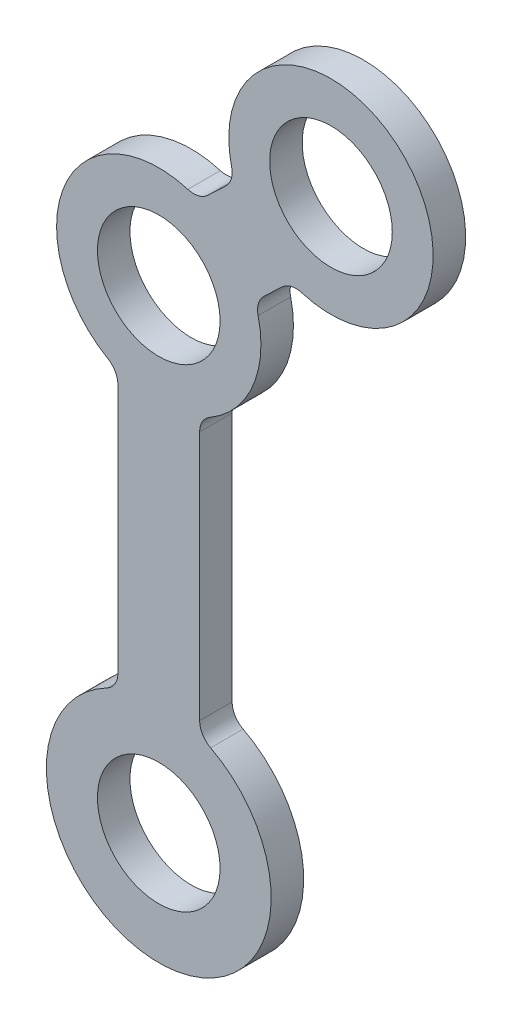
SolidWorks part; units mm, degrees
ref_plane "Front Plane" through (0, 0, 0) normal (0, 0, 1) x (1, 0, 0)
ref_plane "Top Plane" through (0, 0, 0) normal (0, 1, 0) x (1, 0, 0)
ref_plane "Right Plane" through (0, 0, 0) normal (1, 0, 0) x (0, 0, -1)
sketch "Sketch1" plane through (0, 0, 0) normal (0, 0, 1) x (1, 0, 0)
  line L0 (0, 0) -> (0, 23.1951) construction
  line L1 (0, 23.1951) -> (8.4255, 31.1817) construction
  line L3 (5.147, 25.3183) -> (6.0303, 26.1555)
  line L4 (-2, 5.7663) -> (-2, 17.9989)
  line L5 (2.3952, 28.2213) -> (3.2785, 29.0585)
  line L6 (-2, 24.055) -> (7.0496, 32.6332) construction
  line L7 (-2, 0) -> (-2, 24.055) construction
  line L8 (2, 5.7663) -> (2, 17.9989)
  line L9 (2, 0) -> (2, 22.3352) construction
  line L10 (2, 22.3352) -> (9.8014, 29.7302) construction
  circle A0 centre (0, 0) radius 3
  arc A1 (4.1174, 26.8416) -> (4.1166, 26.8425) centre (0, 23.1951) ccw
  circle A2 centre (0, 23.1951) radius 3
  arc A3 (2.5, 18.865) -> (4.8625, 24.3596) centre (0, 23.1951) ccw
  arc A4 (7.0028, 26.3884) -> (3.563, 30.0172) centre (8.4255, 31.1817) ccw
  arc A5 (1.4227, 27.9884) -> (-2.5, 18.865) centre (0, 23.1951) ccw
  arc A6 (-2.5385, 4.8792) -> (2.5385, 4.8792) centre (0, 0) ccw
  arc A7 (2, 17.9989) -> (2.5, 18.865) centre (3, 17.9989) cw
  circle A8 centre (8.4255, 31.1817) radius 3
  arc A9 (5.147, 25.3183) -> (4.8625, 24.3596) centre (5.835, 24.5925) ccw
  arc A10 (2.3952, 28.2213) -> (1.4227, 27.9884) centre (1.7073, 28.9471) cw
  arc A11 (3.563, 30.0172) -> (3.2785, 29.0585) centre (2.5905, 29.7843) cw
  arc A12 (7.0028, 26.3884) -> (6.0303, 26.1555) centre (6.7182, 25.4298) ccw
  arc A13 (-2.5385, 4.8792) -> (-2, 5.7663) centre (-3, 5.7663) ccw
  arc A14 (2.5385, 4.8792) -> (2, 5.7663) centre (3, 5.7663) cw
  arc A15 (-2, 17.9989) -> (-2.5, 18.865) centre (-3, 17.9989) ccw
  point P22 (0.3476, 28.6841)
  point P28 (2, 18.0716)
  point P31 (1.9499, 27.7992)
  point P32 (-2, 18.0716)
  dimension "D1" = 23.1951
  dimension "D4" = 2
  dimension "D6" = 1
  dimension "D7" = 1
  dimension "D8" = 1
  dimension "D9" = 1
  dimension "D10" = 32.3
  dimension "D11" = 1
  dimension "D12" = 1
  dimension "D13" = 1
  dimension "D2" = 2
  dimension "D5" = 1
  dimension "D3" = 11.6093
extrude "Boss-Extrude1" add sketch "Sketch1" along normal blind 1.59
